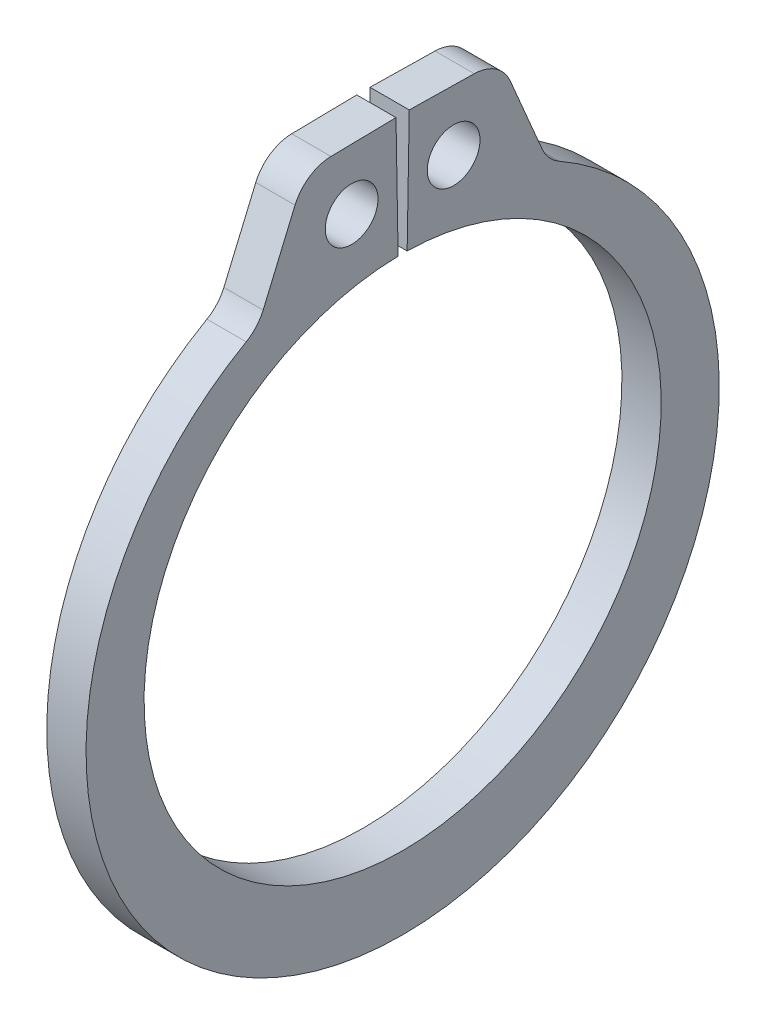
SolidWorks part; units mm, degrees
material "Cast Carbon Steel"
ref_plane "Front" through (0, 0, 0) normal (0, 0, 1) x (1, 0, 0)
ref_plane "Top" through (0, 0, 0) normal (0, 1, 0) x (1, 0, 0)
ref_plane "Right" through (0, 0, 0) normal (1, 0, 0) x (0, 0, -1)
sketch "Sketch1" plane through (0, 0, 0) normal (1, 0, 0) x (0, 0, -1)
  line L0 (0, 0) -> (0, 5.8547) construction
  line L1 (-0.1022, 5.8538) -> (-0.1501, 8.5966)
  line L2 (0.1501, 8.5966) -> (2.2071, 8.5607)
  line L3 (2.2071, 8.5607) -> (3.2813, 6.0365)
  line L4 (0.1022, 5.8538) -> (0.1501, 8.5966)
  line L5 (-0.1501, 8.5966) -> (-2.2071, 8.5607)
  line L6 (-2.2071, 8.5607) -> (-3.2813, 6.0365)
  line L7 (-3.2813, 6.0365) -> (-2.7961, 5.1439) construction
  line L8 (3.2813, 6.0365) -> (2.7961, 5.1439) construction
  line L9 (0, -5.8547) -> (0, -7.5057) construction
  line L10 (-2.2071, 8.5607) -> (-0.1022, 5.8538) construction
  line L11 (0, 5.8547) -> (0, 8.5979) construction
  line L12 (-5.8547, 0) -> (5.8547, 0) construction
  circle A0 centre (0, 0) radius 5.8547 construction
  arc A1 (-0.1022, 5.8538) -> (0.1022, 5.8538) centre (0, 0) ccw
  circle A3 centre (0, 0) radius 9.5885 construction
  circle A4 centre (-1.1547, 7.2072) radius 0.5969
  circle A5 centre (1.1547, 7.2072) radius 0.5969
  arc A6 (-3.2813, 6.0365) -> (3.2813, 6.0365) centre (0, -0.3371) ccw
  point P0 (0, -7.5057)
  dimension "A" = 11.7094
  dimension "D2" = 2.0574
  dimension "L" = 19.177
  dimension "Hole" = 1.1938
  dimension "Smin" = 1.016
  dimension "Smax" = 1.651
  dimension "H" = 2.7432
  dimension "Angle" = 1
extrude "Extrude1" add sketch "Sketch1" along normal mid plane 0.889
fillet "Fillet1" radius 0.9017 4 edges at (0, 6.0365, 3.2813) (0, 6.0365, -3.2813) (0, 8.5607, 2.2071) (0, 8.5607, -2.2071)
sketch "Sketch2" plane through (0, 0, 0) normal (0, 0, 1) x (1, 0, 0)
  line L0 (-4.9403, 0) -> (12.8397, 0)
  line L1 (12.8397, 0) -> (12.8397, -6.35)
  line L2 (-0.4953, -6.35) -> (-4.5339, -6.35)
  line L3 (12.8397, -6.35) -> (0.4953, -6.35)
  line L4 (0.4953, -6.35) -> (0.4953, -5.9436)
  line L5 (0.4953, -5.9436) -> (-0.4953, -5.9436)
  line L6 (-0.4953, -5.9436) -> (-0.4953, -6.35)
  line L7 (-0.4953, -6.35) -> (-4.9403, -6.35) construction
  line L8 (-4.9403, -6.35) -> (-4.9403, 0) construction
  line L9 (12.8397, 0) -> (76.391, 0) construction
  line L10 (-4.5339, -6.35) -> (-4.9403, -5.9436)
  line L11 (-4.9403, -5.9436) -> (-4.9403, 0)
  point P10 (0, -5.9436)
  dimension "D1" = 45
  dimension "Dg" = 11.8872
  dimension "Ds" = 12.7
  dimension "W" = 0.9906
  dimension "D2" = 17.78
  dimension "D3" = 4.445
revolve "Revolve1" [suppressed] add sketch "Sketch2" angle 360 about L9
delete or keep bodies "Body-Delete1" [suppressed] type delete bodies bodies 122
equation "\"D2@Sketch2\" = \"D1@Extrude1\"*20"
equation "\"D3@Sketch2\" = \"D2@Sketch2\"/4"
equation "\"D2@Sketch1\" = \"H@Sketch1\"*.75"
